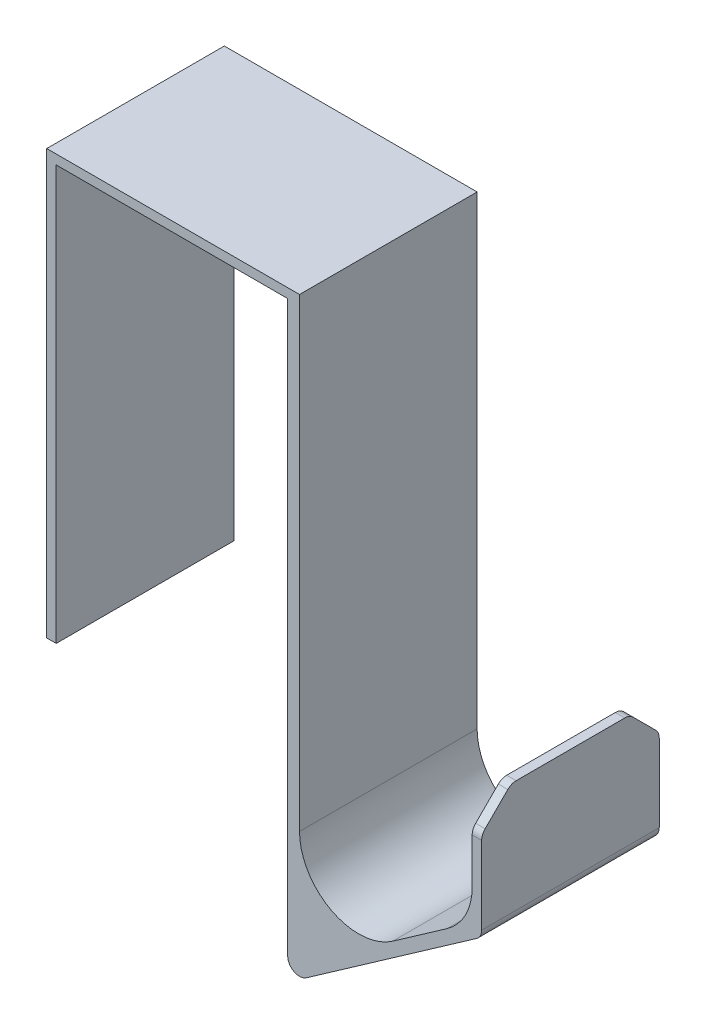
SolidWorks part; units mm, degrees
ref_plane "Plan de face" through (0, 0, 0) normal (0, 0, 1) x (1, 0, 0)
ref_plane "Plan de dessus" through (0, 0, 0) normal (0, 1, 0) x (1, 0, 0)
ref_plane "Plan de droite" through (0, 0, 0) normal (1, 0, 0) x (0, 0, -1)
sketch "Esquisse1" plane through (0, 0, 0) normal (0, 0, 1) x (1, 0, 0)
  line L0 (-19.55, 43.6891) -> (-19.55, 113.6891)
  line L1 (-19.55, 113.6891) -> (19.55, 113.6891)
  line L2 (19.55, 113.6891) -> (19.55, 13.6891)
  line L3 (19.55, 13.6891) -> (52.3161, 36.6321)
  line L4 (52.3161, 36.6321) -> (52.3161, 56.6321)
  line L5 (0, 0) -> (0, 76.9557) construction
  line L6 (-21.15, 43.6891) -> (-21.15, 115.2891)
  line L7 (-21.15, 115.2891) -> (21.55, 115.2891)
  line L8 (21.55, 115.2891) -> (21.55, 17.531)
  line L9 (21.55, 17.531) -> (50.7161, 37.9533)
  line L10 (50.7161, 37.9533) -> (50.7161, 56.6321)
  line L11 (50.7161, 56.6321) -> (52.3161, 56.6321)
  line L12 (-21.15, 43.6891) -> (-19.55, 43.6891)
  point P10 (0, 113.6891)
  dimension "D1" = 39.1
  dimension "D2" = 70
  dimension "D3" = 55
  dimension "D4" = 40
  dimension "D5" = 20
  dimension "D6" = 2
  dimension "D7" = 1.6
  dimension "D8" = 1.6
  dimension "D9" = 1.6
  dimension "D10" = 100
  dimension "D11" = 2
extrude "Boss.-Extru.1" add sketch "Esquisse1" along normal blind 30
fillet "Congé1" radius 10 2 edges at (50.7161, 37.9533, 15) (21.55, 17.531, 15)
chamfer "Chanfrein1" distance 5 angle 45 2 edges at (51.5161, 56.6321, 0) (51.5161, 56.6321, 30)
fillet "Congé2" radius 2 6 edges at (52.3161, 36.6321, 15) (19.55, 13.6891, 15) (51.5161, 51.6321, 30) (51.5161, 51.6321, 0) (51.5161, 56.6321, 5) (51.5161, 56.6321, 25)
